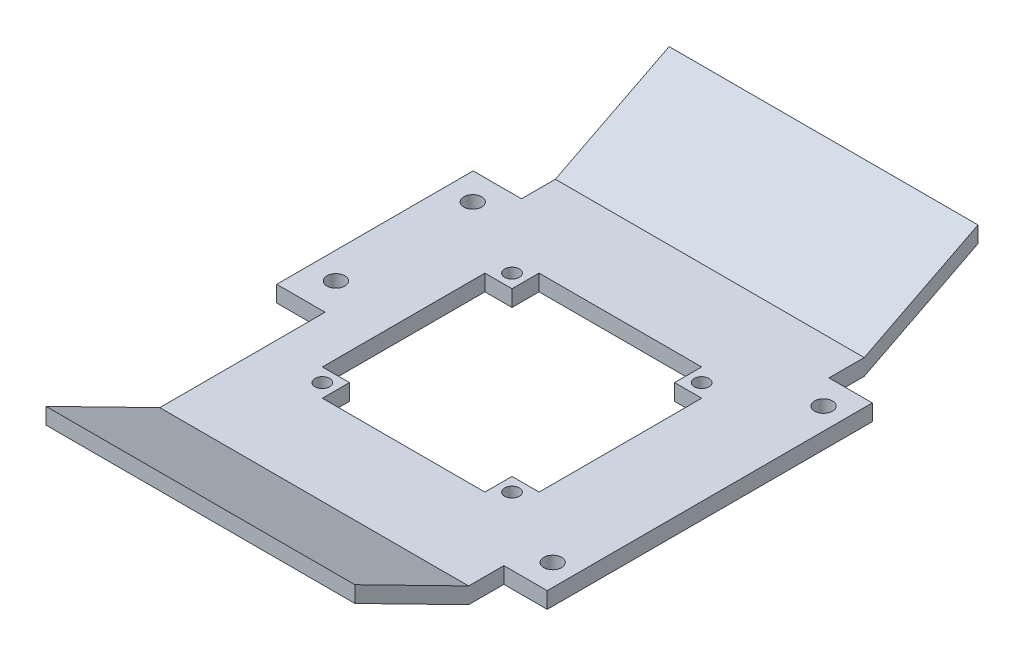
SolidWorks part; units mm, degrees
ref_plane "Front Plane" through (0, 0, 0) normal (0, 0, 1) x (1, 0, 0)
ref_plane "Top Plane" through (0, 0, 0) normal (0, 1, 0) x (1, 0, 0)
ref_plane "Right Plane" through (0, 0, 0) normal (1, 0, 0) x (0, 0, -1)
sketch "Sketch1" plane through (0, 0, 0) normal (1, 0, 0) x (0, 0, -1)
  line L0 (-36.5, 0) -> (36.5, 0)
  line L5 (36.5, 3) -> (-36.5, 3)
  line L6 (-36.5, 3) -> (-57.5, 13.7)
  line L7 (-57.5, 13.7) -> (-57.5, 10.7)
  line L8 (-57.5, 10.7) -> (-36.5, 0)
  line L9 (36.5, 3) -> (57.5, 13.7)
  line L10 (57.5, 13.7) -> (57.5, 10.7)
  line L11 (57.5, 10.7) -> (36.5, 0)
  point P3 (0, 0)
  point P9 (0, 3)
  dimension "D1" = 3
  dimension "D2" = 153
  dimension "D3" = 73
  dimension "D4" = 153
  dimension "D5" = 115
extrude "Boss-Extrude1" add sketch "Sketch1" along normal mid plane 57
sketch "Sketch2" plane through (0, 0, 0) normal (0, 1, 0) x (1, 0, 0)
  line L0 (-15, 20) -> (15, 20)
  line L1 (15, 20) -> (15, 15)
  line L2 (15, 15) -> (20, 15)
  line L3 (20, 15) -> (20, -15)
  line L4 (20, -15) -> (15, -15)
  line L5 (15, -15) -> (15, -20)
  line L6 (15, -20) -> (-15, -20)
  line L7 (-15, -20) -> (-15, -15)
  line L8 (-15, -15) -> (-20, -15)
  line L9 (-20, -15) -> (-20, 15)
  line L10 (-20, 15) -> (-15, 15)
  line L11 (-15, 15) -> (-15, 20)
  circle A0 centre (-17.5, 17.5) radius 1.35
  circle A1 centre (17.5, 17.5) radius 1.35
  circle A2 centre (17.5, -17.5) radius 1.35
  circle A3 centre (-17.5, -17.5) radius 1.35
  point P7 (0, -20)
  point P14 (-20, 0)
  point P18 (-17.5, 15)
  point P20 (-15, 17.5)
  point P28 (0, 0)
  dimension "D3" = 2.7
  dimension "D1" = 40
  dimension "D2" = 5
  dimension "D4" = 4
extrude "Cut-Extrude1" cut sketch "Sketch2" along normal blind 57
sketch "Sketch3" plane through (0, 0, 0) normal (0, 1, 0) x (1, 0, 0)
  line L0 (-28.5, 36.5) -> (-28.5, -36.5) construction
  line L1 (-28.5, 30.2514) -> (-37.4224, 30.2514)
  line L2 (-28.5, 30.2514) -> (-28.5, -6)
  line L5 (28.5, 36.5) -> (28.5, -36.5) construction
  line L6 (28.5, 30) -> (36.5, 30)
  line L7 (28.5, 30) -> (28.5, -30)
  line L8 (28.5, -30) -> (36.5, -30)
  line L9 (36.5, 30) -> (36.5, -30)
  line L11 (-37.4224, 30.2514) -> (-37.4224, -6)
  line L12 (-37.4224, -6) -> (-28.5, -6)
  circle A0 centre (32.5, -25) radius 1.65
  circle A2 centre (32.5, 25) radius 1.65
  circle A4 centre (-32.5, 0) radius 1.65
  circle A5 centre (-32.5, 25.2514) radius 1.65
  point P14 (28.5, 0)
  dimension "D6" = 5
  dimension "D7" = 5
  dimension "D8" = 4
  dimension "D9" = 5
  dimension "D1" = 6
extrude "Boss-Extrude2" add sketch "Sketch3" along normal blind 3
